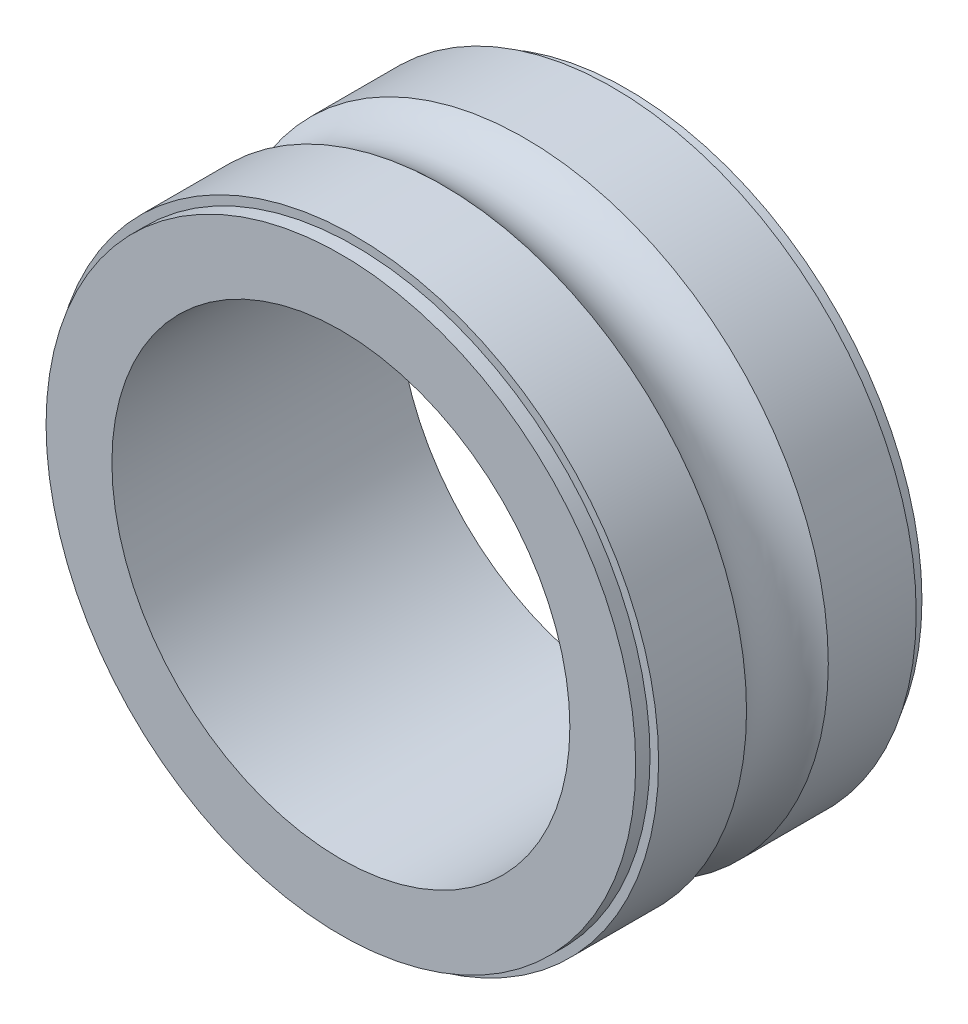
SolidWorks part; units mm, degrees
material "AISI 316 Stainless Steel Sheet (SS)"
ref_plane "Front Plane" through (0, 0, 0) normal (0, 0, 1) x (1, 0, 0)
ref_plane "Top Plane" through (0, 0, 0) normal (0, 1, 0) x (1, 0, 0)
ref_plane "Right Plane" through (0, 0, 0) normal (1, 0, 0) x (0, 0, -1)
sketch "Sketch1" plane through (0, 0, 0) normal (1, 0, 0) x (0, 0, -1)
  line L0 (-6.7554, 0) -> (6.7554, 0) construction
  line L1 (-2.5, 7) -> (-2.5, 7.8) construction
  line L2 (-2.2, 6.7) -> (-2.1, 6.7) construction
  line L3 (-2.3, 8) -> (2.3, 8) construction
  line L5 (-2.5, 6.7) -> (0, 7.35) construction
  line L6 (-2.5, 8) -> (0, 7.35) construction
  line L7 (-2.5, 4) -> (-2.5, 5.3) construction
  line L8 (-2.5, 4) -> (2.5, 4) construction
  line L9 (-2.5, 5.3) -> (-0.7141, 5.3) construction
  line L10 (2.5, 4) -> (2.5, 5.3) construction
  line L11 (-2.5, 4) -> (2.5, 5.3) construction
  line L12 (-2.5, 5.3) -> (2.5, 4) construction
  line L13 (0, 4.65) -> (0, 5) construction
  line L14 (-2.1, 6.7) -> (-2.4, 6.4) construction
  line L15 (-2.5, 7) -> (-2.2, 7) construction
  line L18 (-2.2, 7) -> (-2.2, 6.7) construction
  line L19 (-2.5, 6.7) -> (-2.2, 6.7) construction
  line L20 (-2.4, 6.4) -> (-2.4, 5.2) construction
  line L21 (-2.4, 5.2) -> (-2.3, 5.2) construction
  line L22 (-2.3, 5.2) -> (-2.3, 6.3586) construction
  line L23 (-2.3, 6.3586) -> (-1.9586, 6.7) construction
  line L24 (0, 4.65) -> (0, 0) construction
  line L25 (-1.9586, 6.7) -> (1.9586, 6.7) construction
  line L26 (-2.5, 6.7) -> (-2.5, 7) construction
  line L28 (2.5, 6.7) -> (2.5, 7) construction
  line L29 (2.5, 6.7) -> (2.2, 6.7) construction
  line L30 (2.5, 8) -> (0, 7.35) construction
  line L31 (2.5, 6.7) -> (0, 7.35) construction
  line L32 (2.3, 6.3586) -> (1.9586, 6.7) construction
  line L33 (2.3, 5.2) -> (2.3, 6.3586) construction
  line L34 (2.4, 5.2) -> (2.3, 5.2) construction
  line L35 (2.4, 6.4) -> (2.4, 5.2) construction
  line L36 (2.2, 7) -> (2.2, 6.7) construction
  line L37 (2.5, 7) -> (2.2, 7) construction
  line L38 (2.1, 6.7) -> (2.4, 6.4) construction
  line L39 (2.2, 6.7) -> (2.1, 6.7) construction
  line L40 (2.5, 7) -> (2.5, 7.8) construction
  line L41 (-2.5, 5.15) -> (-2.5, 4)
  line L42 (-2.5, 4) -> (2.5, 4)
  line L44 (-0.7141, 5.3) -> (-2.25, 5.3)
  line L45 (-2.25, 5.3) -> (-2.25, 5.15)
  line L46 (-2.25, 5.15) -> (-2.5, 5.15)
  line L47 (0, 5.3) -> (2.5, 5.3) construction
  line L48 (0, 5.3) -> (0, 7.35) construction
  line L49 (2.5, 5.15) -> (2.5, 4)
  line L50 (2.25, 5.15) -> (2.5, 5.15)
  line L51 (2.25, 5.3) -> (2.25, 5.15)
  line L52 (0.7141, 5.3) -> (2.25, 5.3)
  circle A0 centre (0, 6) radius 1 construction
  arc A1 (-2.5, 7.8) -> (-2.3, 8) centre (-2.3, 7.8) cw construction
  arc A2 (2.5, 7.8) -> (2.3, 8) centre (2.3, 7.8) ccw construction
  arc A3 (-0.7141, 5.3) -> (0.7141, 5.3) centre (0, 6) ccw
  point P3 (0, 7.35)
  point P4 (0, 0)
  point P12 (0, 4.65)
  point P31 (-2.35, 5.2)
  dimension "D3" = 2
  dimension "D14" = 0.2
  dimension "D1" = 8
  dimension "D2" = 5
  dimension "D4" = 5
  dimension "D5" = 4
  dimension "D6" = 1.3
  dimension "D7" = 0.3
  dimension "D8" = 0.3
  dimension "D9" = 45
  dimension "D10" = 0.1
  dimension "D11" = 0.1
  dimension "D12" = 0.1
  dimension "D13" = 0.1
  dimension "D15" = 0.2
  dimension "D16" = 0.05
  dimension "D17" = 0.05
  dimension "D18" = 1.3
revolve "Revolve1" add sketch "Sketch1" angle 360 about L0
